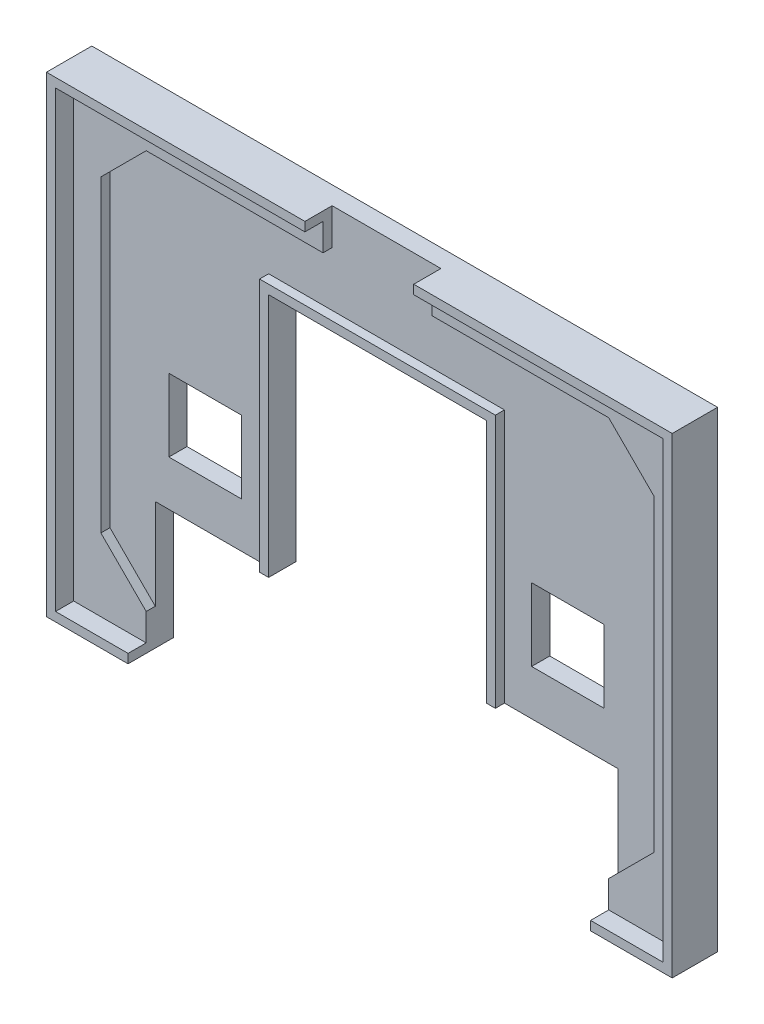
SolidWorks part; units mm, degrees
ref_plane "Přední rovina" through (0, 0, 0) normal (0, 0, 1) x (1, 0, 0)
ref_plane "Horní rovina" through (0, 0, 0) normal (0, 1, 0) x (1, 0, 0)
ref_plane "Pravá rovina" through (0, 0, 0) normal (1, 0, 0) x (0, 0, -1)
sketch "Skica1" plane through (0, 0, 0) normal (0, 0, 1) x (1, 0, 0)
  line L1 (-33.5, -25) -> (33.5, -25)
  line L2 (-33.5, -25) -> (-33.5, 25)
  line L3 (-33.5, 25) -> (33.5, 25)
  line L4 (33.5, -25) -> (33.5, 25)
  line L5 (-33.5, -25) -> (33.5, 25) construction
  line L6 (-33.5, 25) -> (33.5, -25) construction
  point P0 (0, 0)
  dimension "D1" = 67
  dimension "D2" = 50
extrude "Přidat vysunutím1" add sketch "Skica1" along normal blind 3
sketch "Skica2" plane through (0, 0, 3) normal (0, 0, 1) x (1, 0, 0)
  line L0 (-1000, 0) -> (49000, 0) construction
  line L1 (0, -1000) -> (0, 49000) construction
  line L2 (-1000, -22) -> (49000, -22) construction
  line L3 (-25.5, -1000) -> (-25.5, 49000) construction
  line L4 (-30.5, -1000) -> (-30.5, 49000) construction
  line L6 (-33.5, -25) -> (33.5, -25) construction
  line L7 (-25.5, -22) -> (-30.5, -17)
  line L8 (-30.5, -17) -> (-30.5, 17)
  line L9 (-25.5, -22) -> (25.5, -22)
  line L10 (30.5, -17) -> (30.5, 17)
  line L11 (25.5, -22) -> (30.5, -17)
  line L12 (25.5, 22) -> (30.5, 17)
  line L13 (-25.5, 22) -> (25.5, 22)
  line L14 (-25.5, 22) -> (-30.5, 17)
  point P20 (0, -22)
  point P21 (30.5, 0)
  point P24 (-30.5, 0)
  dimension "D1" = 30.5
  dimension "D2" = 5
  dimension "D3" = 3
  dimension "D4" = 45
extrude "Odebrat vysunutím1" cut sketch "Skica2" against normal offset from surface (1 mm away) 2 up to face at (0, 0, 0)
sketch "Skica3" plane through (0, 0, 0) normal (0, 0, -1) x (-1, 0, 0)
  line L0 (0, -1000) -> (0, 49000) construction
  line L1 (33.5, -25) -> (-33.5, -25) construction
  line L2 (24, 1) -> (16, 1)
  line L3 (24, 1) -> (24, -7)
  line L4 (24, -7) -> (16, -7)
  line L5 (16, 1) -> (16, -7)
  line L6 (-16, 1) -> (-16, -7)
  line L7 (33.5, -25) -> (-33.5, -25) construction
  line L8 (25.5, -25) -> (-25.5, -25)
  line L9 (25.5, -25) -> (25.5, -12)
  line L11 (-25.5, -25) -> (-25.5, -12)
  line L12 (-24, -7) -> (-16, -7)
  line L13 (25.5, -12) -> (12, -12)
  line L15 (12, -12) -> (12, 15)
  line L16 (12, 15) -> (-12, 15)
  line L17 (-12, -12) -> (-12, 15)
  line L18 (-12, -12) -> (-25.5, -12)
  line L19 (-24, 1) -> (-24, -7)
  line L20 (-24, 1) -> (-16, 1)
  dimension "D1" = 16
  dimension "D2" = 8
  dimension "D3" = 18
  dimension "D4" = 13
  dimension "D5" = 51
  dimension "D6" = 24
  dimension "D7" = 27
extrude "Odebrat vysunutím2" cut sketch "Skica3" against normal through all
sketch "Skica4" plane through (0, 0, 2) normal (0, 0, 1) x (1, 0, 0)
  line L0 (12, 15) -> (12, -12) construction
  line L1 (-12, -12) -> (-12, 15) construction
  line L2 (-12, 15) -> (12, 15) construction
  line L3 (12, 15) -> (12, -12)
  line L4 (-12, -12) -> (-12, 15)
  line L5 (-12, 15) -> (12, 15)
extrude "Vysunout tenkostěnný1" add sketch "Skica4" along normal up to surface (1 mm away) thin up to face at (0, -3.5714, 3) thin type one direction reverse wall 1
sketch "Skica5" plane through (0, 0, 0) normal (0, 0, -1) x (-1, 0, 0)
  line L0 (-33.5, 25) -> (33.5, 25) construction
  line L1 (33.5, 25) -> (33.5, -25) construction
  line L2 (33.5, -25) -> (25.5, -25) construction
  line L3 (-33.5, -25) -> (-33.5, 25) construction
  line L4 (-25.5, -25) -> (-33.5, -25) construction
  line L5 (-33.5, 25) -> (33.5, 25)
  line L6 (33.5, 25) -> (33.5, -25)
  line L7 (33.5, -25) -> (25.5, -25)
  line L8 (-33.5, -25) -> (-33.5, 25)
  line L9 (-25.5, -25) -> (-33.5, -25)
extrude "Vysunout tenkostěnný2" add sketch "Skica5" against normal blind 5 thin thin type one direction reverse wall 1
sketch "Skica6" plane through (0, 0, 2) normal (0, 0, 1) x (1, 0, 0)
  line L0 (0, -1000) -> (0, 49000) construction
  line L1 (25.5, 22) -> (-25.5, 22) construction
  line L2 (-6, 22) -> (6, 22)
  line L3 (-6, 22) -> (-6, 26)
  line L4 (-6, 26) -> (6, 26)
  line L5 (6, 22) -> (6, 26)
  line L6 (34.5, 26) -> (-34.5, 26) construction
  dimension "D1" = 12
extrude "Odebrat vysunutím3" cut sketch "Skica6" along normal through all
sketch "Skica7" plane through (0, 0, 0) normal (0, 0, -1) x (-1, 0, 0)
  line L0 (-27.5735, 21.5358) -> (-25.7356, 21.5358)
  line L1 (-25.7356, 21.5358) -> (-25.7356, 19.6626)
  line L2 (-25.7356, 19.6626) -> (-20.7522, 19.6626)
  line L3 (-20.7522, 19.6626) -> (-20.7522, 21.5358)
  line L4 (-20.7522, 21.5358) -> (-18.8436, 21.5358)
  line L5 (-18.8436, 21.5358) -> (-18.8436, 18.0014)
  line L6 (-18.8436, 18.0014) -> (-17.1118, 18.0014)
  line L7 (-17.1118, 18.0014) -> (-17.1118, 16.2696)
  line L8 (-17.1118, 16.2696) -> (-15.38, 16.2696)
  line L9 (-15.38, 16.2696) -> (-15.38, 7.4337)
  line L11 (-17.1118, 7.4337) -> (-17.1118, 10.862)
  line L12 (-17.1118, 10.862) -> (-18.8436, 10.862)
  line L13 (-18.8436, 10.862) -> (-18.8436, 5.7372)
  line L14 (-18.8436, 5.7372) -> (-22.378, 5.7372)
  line L18 (-20.6108, 9.0772) -> (-25.7356, 9.0772)
  line L19 (-25.7356, 9.0772) -> (-25.7356, 7.4337)
  line L20 (-25.7356, 7.4337) -> (-23.9685, 7.4337)
  line L21 (-23.9685, 7.4337) -> (-23.9685, 5.7372)
  line L22 (-23.9685, 5.7372) -> (-27.5735, 5.7372)
  line L23 (-27.5735, 5.7372) -> (-27.5735, 10.862)
  line L24 (-27.5735, 10.862) -> (-29.3407, 10.862)
  line L25 (-29.3407, 10.862) -> (-29.3407, 7.4337)
  line L27 (-31.1079, 7.4337) -> (-31.1079, 16.2696)
  line L28 (-31.1079, 16.2696) -> (-29.3407, 16.2696)
  line L29 (-29.3407, 16.2696) -> (-29.3407, 18.0014)
  line L30 (-29.3407, 18.0014) -> (-27.5735, 18.0014)
  line L31 (-27.5735, 18.0014) -> (-27.5735, 21.5358)
  line L32 (-22.378, 5.7372) -> (-22.378, 7.4337)
  line L33 (-22.378, 7.4337) -> (-20.6108, 7.4337)
  line L34 (-20.6108, 7.4337) -> (-20.6108, 9.0772)
  line L35 (-31.1079, 7.4337) -> (-29.3407, 7.4337)
  line L36 (-17.1118, 7.4337) -> (-15.38, 7.4337)
  line L37 (34.5, 26) -> (34.5, -26) construction
  line L38 (34.5, -26) -> (25.5, -26) construction
  line L39 (0, 0) -> (0, 33.9491) construction
  line L40 (22.378, 7.4337) -> (20.6108, 7.4337)
  line L41 (22.378, 5.7372) -> (22.378, 7.4337)
  line L42 (18.8436, 5.7372) -> (22.378, 5.7372)
  line L43 (18.8436, 10.862) -> (18.8436, 5.7372)
  line L44 (17.1118, 10.862) -> (18.8436, 10.862)
  line L45 (17.1118, 7.4337) -> (17.1118, 10.862)
  line L46 (15.38, 7.4337) -> (17.1118, 7.4337)
  line L47 (15.38, 16.2696) -> (15.38, 7.4337)
  line L48 (17.1118, 16.2696) -> (15.38, 16.2696)
  line L49 (17.1118, 18.0014) -> (17.1118, 16.2696)
  line L50 (18.8436, 18.0014) -> (17.1118, 18.0014)
  line L51 (18.8436, 21.5358) -> (18.8436, 18.0014)
  line L52 (20.7522, 21.5358) -> (18.8436, 21.5358)
  line L53 (20.7522, 19.6626) -> (20.7522, 21.5358)
  line L54 (25.7356, 19.6626) -> (20.7522, 19.6626)
  line L55 (25.7356, 21.5358) -> (25.7356, 19.6626)
  line L56 (27.5735, 21.5358) -> (25.7356, 21.5358)
  line L57 (27.5735, 18.0014) -> (27.5735, 21.5358)
  line L58 (29.3407, 18.0014) -> (27.5735, 18.0014)
  line L59 (29.3407, 16.2696) -> (29.3407, 18.0014)
  line L60 (31.1079, 16.2696) -> (29.3407, 16.2696)
  line L61 (31.1079, 7.4337) -> (31.1079, 16.2696)
  line L62 (29.3407, 7.4337) -> (31.1079, 7.4337)
  line L63 (29.3407, 10.862) -> (29.3407, 7.4337)
  line L64 (27.5735, 10.862) -> (29.3407, 10.862)
  line L65 (27.5735, 5.7372) -> (27.5735, 10.862)
  line L66 (23.9685, 5.7372) -> (27.5735, 5.7372)
  line L67 (23.9685, 7.4337) -> (23.9685, 5.7372)
  line L68 (25.7356, 7.4337) -> (23.9685, 7.4337)
  line L69 (25.7356, 9.0772) -> (25.7356, 7.4337)
  line L70 (20.6108, 9.0772) -> (25.7356, 9.0772)
  line L71 (20.6108, 7.4337) -> (20.6108, 9.0772)
  line L72 (-34.5, -26) -> (-34.5, 26) construction
  line L73 (-25.5, -26) -> (-34.5, -26) construction
  dimension "D1" = 3.3921
  dimension "D2" = 5.1593
  dimension "D3" = 8.7644
  dimension "D4" = 12.122
  dimension "D5" = 13.7478
  dimension "D6" = 15.6564
  dimension "D7" = 17.3882
  dimension "D8" = 31.7372
  dimension "D9" = 33.4337
  dimension "D10" = 35.0772
  dimension "D11" = 42.2696
  dimension "D12" = 45.6626
extrude "Odebrat vysunutím4" cut sketch "Skica7" against normal blind 1
sketch "Skica8" plane through (0, 0, 1) normal (0, 0, -1) x (-1, 0, 0)
  line L0 (-27.5735, 21.5358) -> (-27.5735, 18.0014) construction
  line L1 (-27.5735, 16.2696) -> (-25.7356, 16.2696)
  line L2 (-27.5735, 16.2696) -> (-27.5735, 12.8234)
  line L3 (-27.5735, 12.8234) -> (-25.7356, 12.8234)
  line L4 (-25.7356, 16.2696) -> (-25.7356, 12.8234)
  line L5 (-25.7356, 19.6626) -> (-25.7356, 21.5358) construction
  line L6 (-29.3407, 16.2696) -> (-31.1079, 16.2696) construction
  line L7 (-23.1732, 9.0772) -> (-23.1732, 21.3524) construction
  line L8 (-25.7356, 9.0772) -> (-20.6108, 9.0772) construction
  line L10 (-25.7356, 9.0772) -> (-20.6108, 9.0772) construction
  line L11 (-18.773, 12.8234) -> (-20.6108, 12.8234)
  line L12 (-20.6108, 16.2696) -> (-20.6108, 12.8234)
  line L13 (-18.773, 16.2696) -> (-20.6108, 16.2696)
  line L14 (-18.773, 16.2696) -> (-18.773, 12.8234)
  line L15 (0, 0) -> (0, 33.5125) construction
  line L16 (27.5735, 12.8234) -> (25.7356, 12.8234)
  line L17 (25.7356, 16.2696) -> (25.7356, 12.8234)
  line L18 (27.5735, 16.2696) -> (25.7356, 16.2696)
  line L19 (27.5735, 16.2696) -> (27.5735, 12.8234)
  line L20 (18.773, 16.2696) -> (18.773, 12.8234)
  line L21 (18.773, 16.2696) -> (20.6108, 16.2696)
  line L22 (20.6108, 16.2696) -> (20.6108, 12.8234)
  line L23 (18.773, 12.8234) -> (20.6108, 12.8234)
  dimension "D1" = 0
  dimension "D2" = 0
  dimension "D3" = 0
  dimension "D4" = 3.7463
extrude "Přidat vysunutím2" add sketch "Skica8" along normal blind 1
sketch "Skica9" plane through (0, 0, 0) normal (0, 0, -1) x (-1, 0, 0)
  line L0 (22.378, 5.7372) -> (22.378, 7.4337) construction
  line L1 (18.8436, 5.7372) -> (22.378, 5.7372) construction
  text T0 "ALIN\r\n" font "BLOXAT" height 5.8
  dimension "D1" = 32.9595
  dimension "D2" = 11.7672
extrude "Odebrat vysunutím5" cut sketch "Skica9" against normal blind 1
